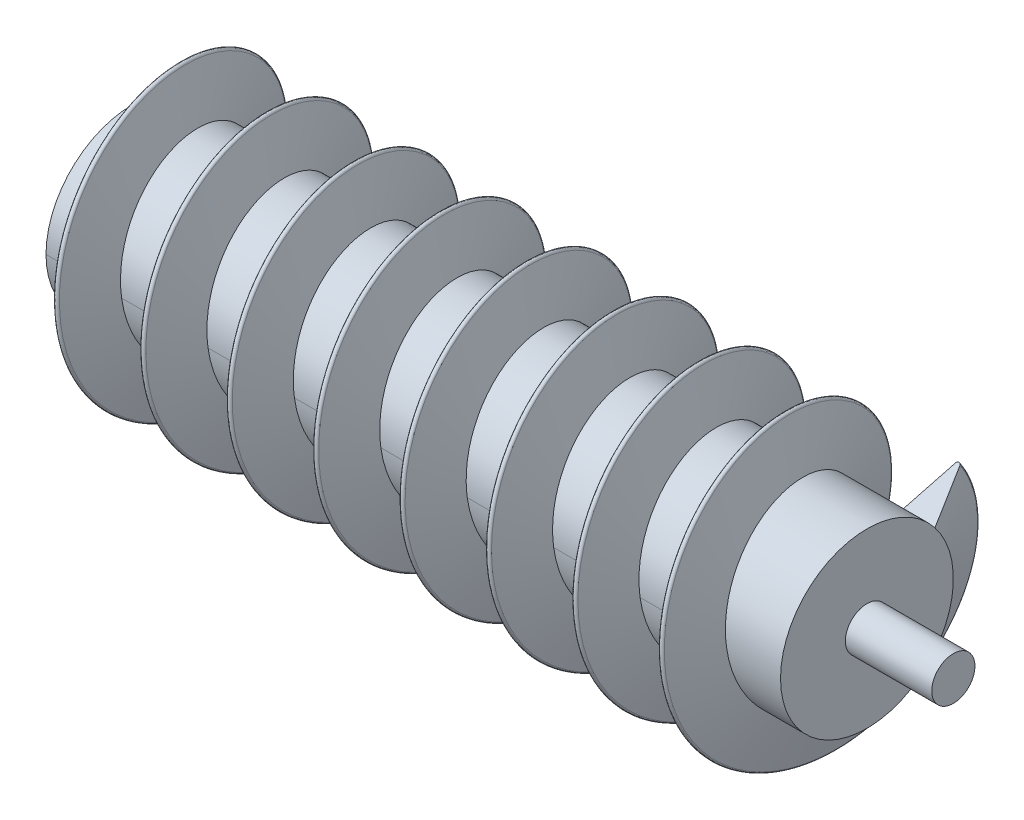
SolidWorks part; units mm, degrees
ref_plane "Front Plane" through (0, 0, 0) normal (0, 0, 1) x (1, 0, 0)
ref_plane "Top Plane" through (0, 0, 0) normal (0, 1, 0) x (1, 0, 0)
ref_plane "Right Plane" through (0, 0, 0) normal (1, 0, 0) x (0, 0, -1)
sketch "Sketch1" plane through (0, 0, 0) normal (0, 0, 1) x (1, 0, 0)
  line L0 (0, 0) -> (199.5771, 0) construction
  line L1 (0, 0) -> (190, 0)
  line L2 (0, 20) -> (170, 20)
  line L3 (0, 20) -> (0, 0)
  line L5 (170, 20) -> (170, 5)
  line L8 (170, 5) -> (190, 5)
  line L9 (190, 0) -> (190, 5)
  dimension "D1" = 170
  dimension "D2" = 20
  dimension "D4" = 5
  dimension "D5" = 20
revolve "Revolve1" add sketch "Sketch1" angle 360 about L0
sketch "Sketch3" plane through (0, 0, 0) normal (-1, 0, 0) x (0, 0, 1)
  circle A0 centre (0, 0) radius 31.5
  dimension "D1" = 63
curve "Helix/Spiral1" pitch 20 height 162 turns 8.1
sketch "Sketch12" plane through (0, 0, 0) normal (0, 1, 0) x (1, 0, 0)
  line L0 (0, 20) -> (3.3161, 31.1018)
  line L1 (4.3585, 31.0943) -> (7.5, 20)
  line L2 (7.5, 20) -> (7.5, 18.9551)
  line L3 (7.5, 18.9551) -> (0, 18.9551)
  line L4 (0, 20) -> (0, 18.9551)
  line L6 (0, 31.5008) -> (3.3161, 31.5008) construction
  line L7 (170, 20) -> (0, 20) construction
  arc A0 (3.3161, 31.1018) -> (4.3585, 31.0943) centre (3.8362, 30.9464) cw
  dimension "D1" = 7.5
sweep "Sweep4" add profiles "Sketch12" path "Helix/Spiral1"
